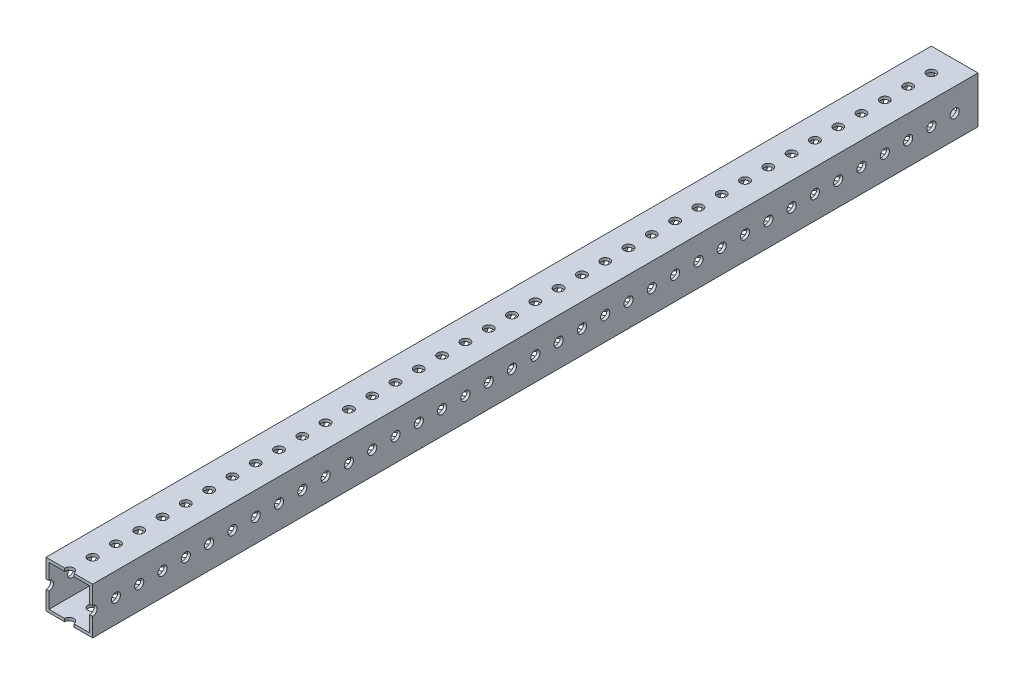
SolidWorks part; units mm, degrees
material "6061 Alloy"
ref_plane "Front Plane" through (0, 0, 0) normal (0, 0, 1) x (1, 0, 0)
ref_plane "Top Plane" through (0, 0, 0) normal (0, 1, 0) x (1, 0, 0)
ref_plane "Right Plane" through (0, 0, 0) normal (1, 0, 0) x (0, 0, -1)
sketch "Sketch1" plane through (0, 0, 0) normal (0, 0, 1) x (1, 0, 0)
  line L0 (1.5875, 1.5875) -> (23.8125, 1.5875)
  line L1 (0, 0) -> (25.4, 0)
  line L2 (0, 0) -> (0, 25.4)
  line L3 (0, 25.4) -> (25.4, 25.4)
  line L4 (25.4, 0) -> (25.4, 25.4)
  line L5 (23.8125, 1.5875) -> (23.8125, 23.8125)
  line L6 (1.5875, 23.8125) -> (23.8125, 23.8125)
  line L7 (1.5875, 1.5875) -> (1.5875, 23.8125)
  dimension "D1" = 25.4
  dimension "D2" = 1.5875
extrude "Boss-Extrude1" add sketch "Sketch1" along normal blind 482.6
sketch "Sketch2" plane through (0, 25.4, 0) normal (0, 1, 0) x (1, 0, 0)
  line L0 (25.4, -482.6) -> (25.4, 0) construction
  line L1 (25.4, 0) -> (0, 0) construction
  line L2 (12.7, -12.7) -> (12.7, -25.4) construction
  circle A0 centre (12.7, -12.7) radius 2.4892
  circle A1 centre (12.7, -25.4) radius 2.4892
  circle A2 centre (12.7, -38.1) radius 2.4892
  circle A3 centre (12.7, -50.8) radius 2.4892
  circle A4 centre (12.7, -63.5) radius 2.4892
  circle A5 centre (12.7, -76.2) radius 2.4892
  circle A6 centre (12.7, -88.9) radius 2.4892
  circle A7 centre (12.7, -101.6) radius 2.4892
  circle A8 centre (12.7, -114.3) radius 2.4892
  circle A9 centre (12.7, -127) radius 2.4892
  circle A10 centre (12.7, -139.7) radius 2.4892
  circle A11 centre (12.7, -152.4) radius 2.4892
  circle A12 centre (12.7, -165.1) radius 2.4892
  circle A13 centre (12.7, -177.8) radius 2.4892
  circle A14 centre (12.7, -190.5) radius 2.4892
  circle A15 centre (12.7, -203.2) radius 2.4892
  circle A16 centre (12.7, -215.9) radius 2.4892
  circle A17 centre (12.7, -228.6) radius 2.4892
  circle A18 centre (12.7, -241.3) radius 2.4892
  circle A19 centre (12.7, -254) radius 2.4892
  circle A20 centre (12.7, -266.7) radius 2.4892
  circle A21 centre (12.7, -279.4) radius 2.4892
  circle A22 centre (12.7, -292.1) radius 2.4892
  circle A23 centre (12.7, -304.8) radius 2.4892
  circle A24 centre (12.7, -317.5) radius 2.4892
  circle A25 centre (12.7, -330.2) radius 2.4892
  circle A26 centre (12.7, -342.9) radius 2.4892
  circle A27 centre (12.7, -355.6) radius 2.4892
  circle A28 centre (12.7, -368.3) radius 2.4892
  circle A29 centre (12.7, -381) radius 2.4892
  circle A30 centre (12.7, -393.7) radius 2.4892
  circle A31 centre (12.7, -406.4) radius 2.4892
  circle A32 centre (12.7, -419.1) radius 2.4892
  circle A33 centre (12.7, -431.8) radius 2.4892
  circle A34 centre (12.7, -444.5) radius 2.4892
  circle A35 centre (12.7, -457.2) radius 2.4892
  circle A36 centre (12.7, -469.9) radius 2.4892
  circle A37 centre (12.7, -482.6) radius 2.4892
  circle A38 centre (12.7, -495.3) radius 2.4892
  circle A39 centre (12.7, -508) radius 2.4892
  circle A40 centre (12.7, -520.7) radius 2.4892
  circle A41 centre (12.7, -533.4) radius 2.4892
  circle A42 centre (12.7, -546.1) radius 2.4892
  circle A43 centre (12.7, -558.8) radius 2.4892
  dimension "D1" = 4.9784
  dimension "D2" = 12.7
  dimension "D3" = 12.7
  dimension "D5" = 12.7
  dimension "D4" = 44
extrude "Cut-Extrude1" cut sketch "Sketch2" against normal through all
sketch "Sketch3" plane through (25.4, 0, 0) normal (1, 0, 0) x (0, 0, -1)
  line L0 (0, 0) -> (0, 25.4) construction
  line L1 (-482.6, 25.4) -> (0, 25.4) construction
  line L2 (-12.7, 12.7) -> (-25.4, 12.7) construction
  circle A0 centre (-12.7, 12.7) radius 2.4892
  circle A1 centre (-25.4, 12.7) radius 2.4892
  circle A2 centre (-38.1, 12.7) radius 2.4892
  circle A3 centre (-50.8, 12.7) radius 2.4892
  circle A4 centre (-63.5, 12.7) radius 2.4892
  circle A5 centre (-76.2, 12.7) radius 2.4892
  circle A6 centre (-88.9, 12.7) radius 2.4892
  circle A7 centre (-101.6, 12.7) radius 2.4892
  circle A8 centre (-114.3, 12.7) radius 2.4892
  circle A9 centre (-127, 12.7) radius 2.4892
  circle A10 centre (-139.7, 12.7) radius 2.4892
  circle A11 centre (-152.4, 12.7) radius 2.4892
  circle A12 centre (-165.1, 12.7) radius 2.4892
  circle A13 centre (-177.8, 12.7) radius 2.4892
  circle A14 centre (-190.5, 12.7) radius 2.4892
  circle A15 centre (-203.2, 12.7) radius 2.4892
  circle A16 centre (-215.9, 12.7) radius 2.4892
  circle A17 centre (-228.6, 12.7) radius 2.4892
  circle A18 centre (-241.3, 12.7) radius 2.4892
  circle A19 centre (-254, 12.7) radius 2.4892
  circle A20 centre (-266.7, 12.7) radius 2.4892
  circle A21 centre (-279.4, 12.7) radius 2.4892
  circle A22 centre (-292.1, 12.7) radius 2.4892
  circle A23 centre (-304.8, 12.7) radius 2.4892
  circle A24 centre (-317.5, 12.7) radius 2.4892
  circle A25 centre (-330.2, 12.7) radius 2.4892
  circle A26 centre (-342.9, 12.7) radius 2.4892
  circle A27 centre (-355.6, 12.7) radius 2.4892
  circle A28 centre (-368.3, 12.7) radius 2.4892
  circle A29 centre (-381, 12.7) radius 2.4892
  circle A30 centre (-393.7, 12.7) radius 2.4892
  circle A31 centre (-406.4, 12.7) radius 2.4892
  circle A32 centre (-419.1, 12.7) radius 2.4892
  circle A33 centre (-431.8, 12.7) radius 2.4892
  circle A34 centre (-444.5, 12.7) radius 2.4892
  circle A35 centre (-457.2, 12.7) radius 2.4892
  circle A36 centre (-469.9, 12.7) radius 2.4892
  circle A37 centre (-482.6, 12.7) radius 2.4892
  circle A38 centre (-495.3, 12.7) radius 2.4892
  circle A39 centre (-508, 12.7) radius 2.4892
  circle A40 centre (-520.7, 12.7) radius 2.4892
  circle A41 centre (-533.4, 12.7) radius 2.4892
  circle A42 centre (-546.1, 12.7) radius 2.4892
  circle A43 centre (-558.8, 12.7) radius 2.4892
  dimension "D1" = 12.7
  dimension "D2" = 12.7
  dimension "D3" = 4.9784
  dimension "D5" = 12.7
  dimension "D4" = 44
extrude "Cut-Extrude2" cut sketch "Sketch3" against normal through all
